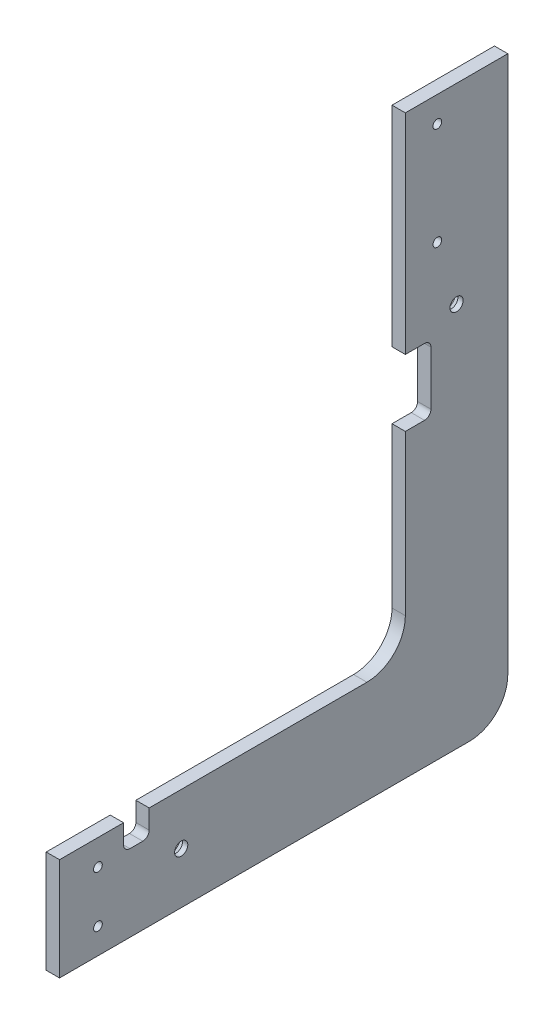
SolidWorks part; units mm, degrees
material "Acrylic (BLUE)"
ref_plane "Front Plane" through (0, 0, 0) normal (0, 0, 1) x (1, 0, 0)
ref_plane "Top Plane" through (0, 0, 0) normal (0, 1, 0) x (1, 0, 0)
ref_plane "Right Plane" through (0, 0, 0) normal (1, 0, 0) x (0, 0, -1)
sketch "Sketch1" plane through (0, 0, 0) normal (1, 0, 0) x (0, 0, -1)
  line L0 (-222.25, 0) -> (-171.45, 0)
  line L1 (-165.1, 0) -> (165.1, 0) construction
  line L2 (-165.1, 0) -> (-165.1, -228.6) construction
  line L3 (-165.1, -228.6) -> (165.1, -228.6) construction
  line L4 (165.1, 0) -> (165.1, -228.6) construction
  line L5 (171.45, 0) -> (222.25, 0)
  line L6 (-171.45, 0) -> (-171.45, -215.9)
  line L7 (-152.4, -234.95) -> (152.4, -234.95)
  line L8 (171.45, 0) -> (171.45, -215.9)
  line L9 (-165.1, 0) -> (-165.1, 25.4) construction
  line L10 (-222.25, 0) -> (-222.25, -266.7)
  line L11 (-203.2, -285.75) -> (203.2, -285.75)
  line L12 (222.25, 0) -> (222.25, -266.7)
  line L13 (-165.1, 25.4) -> (165.1, 25.4) construction
  line L14 (165.1, 25.4) -> (165.1, 0) construction
  line L15 (0, -234.95) -> (0, -285.75)
  arc A0 (203.2, -285.75) -> (222.25, -266.7) centre (203.2, -266.7) ccw
  arc A1 (-203.2, -285.75) -> (-222.25, -266.7) centre (-203.2, -266.7) cw
  arc A2 (171.45, -215.9) -> (152.4, -234.95) centre (152.4, -215.9) cw
  arc A3 (-152.4, -234.95) -> (-171.45, -215.9) centre (-152.4, -215.9) cw
  dimension "D8" = 19.05
  dimension "D1" = 50.8
  dimension "D2" = 330.2
  dimension "D3" = 228.6
  dimension "D4" = 6.35
  dimension "D5" = 6.35
  dimension "D6" = 6.35
  dimension "D7" = 50.8
  dimension "D9" = 254
  dimension "D10" = 25.4
  dimension "D11" = 285.75
extrude "Boss-Extrude2" add sketch "Sketch1" along normal blind 6.604 contours L8 A2 L7 L15 L11 A0 L12 L5
hole_wizard "CSK for #8 Flat Head Socket Cap Screw1" positions "Sketch4" profile "Sketch5" countersink size "#8" standard "ANSI Inch" end condition through all
sketch "Sketch4" plane through (0, -130.0171, -32.7853) normal (-1, 0, 0) x (0, 0, 1)
  line L15 (-154.5397, 117.3171) -> (-154.5397, 66.5171) construction
  line L16 (-154.5397, 66.5171) -> (-154.5397, 53.8171) construction
  line L18 (-154.5397, 117.3171) -> (-154.5397, 130.0171) construction
  line L20 (-138.6647, 130.0171) -> (-138.6647, -85.8829) construction
  line L21 (-138.6647, 130.0171) -> (-189.4647, 130.0171) construction
  point P37 (-154.5397, 117.3171)
  point P39 (-154.5397, 66.5171)
  dimension "D1" = 15.875
  dimension "D2" = 76.2
  dimension "D3" = 12.7
sketch "Sketch5" plane through (0, -12.7, -187.325) normal (0, 1, 0) x (0, 0, 1)
  line L0 (0, 0) -> (0, 6.604)
  line L1 (0, 6.604) -> (2.1526, 6.604)
  line L2 (2.1526, 6.604) -> (2.1526, 2.7685)
  line L3 (2.1526, 2.7685) -> (4.5593, 0)
  line L5 (4.5593, 0) -> (0, 0)
  line L6 (-2.1526, 2.7685) -> (-4.5593, 0) construction
  line L11 (0, -6.35) -> (0, 107.95) construction
  dimension "Thru Hole Dia." = 4.3053
  dimension "Thru Hole Depth" = 6.604
  dimension "Near C'Sink Dia." = 9.1186
  dimension "Near C'Sink Angle" = 82
hole_wizard "CSK for #8 Flat Head Socket Cap Screw2" positions "Sketch8" profile "Sketch7" countersink size "#8" standard "ANSI Inch" end condition through all
sketch "Sketch8" plane through (0, 131.5943, -188.0745) normal (-1, 0, 0) x (0, 0, 1)
  line L1 (169.0245, -366.5443) -> (169.0245, -379.2443) construction
  line L2 (188.0745, -366.5443) -> (35.6745, -366.5443) construction
  line L3 (169.0245, -379.2443) -> (169.0245, -404.6443) construction
  line L4 (169.0245, -404.6443) -> (169.0245, -417.3443) construction
  line L5 (188.0745, -417.3443) -> (-15.1255, -417.3443) construction
  line L6 (188.0745, -366.5443) -> (188.0745, -417.3443) construction
  point P3 (169.0245, -379.2443)
  point P7 (169.0245, -404.6443)
  dimension "D1" = 12.7
  dimension "D2" = 19.05
sketch "Sketch7" plane through (0, -247.65, -19.05) normal (0, 1, 0) x (0, 0, 1)
  line L0 (0, 0) -> (0, 6.604)
  line L1 (0, 6.604) -> (2.1526, 6.604)
  line L2 (2.1526, 6.604) -> (2.1526, 2.7685)
  line L3 (2.1526, 2.7685) -> (4.5593, 0)
  line L5 (4.5593, 0) -> (0, 0)
  line L6 (-2.1526, 2.7685) -> (-4.5593, 0) construction
  line L11 (0, -6.35) -> (0, 107.95) construction
  dimension "Thru Hole Dia." = 4.3053
  dimension "Thru Hole Depth" = 6.604
  dimension "Near C'Sink Dia." = 9.1186
  dimension "Near C'Sink Angle" = 82
hole_wizard "CSK for 1/4 Flat Head Socket Cap Screw1" positions "Sketch10" profile "Sketch9" countersink size "1/4" standard "ANSI Inch" end condition through all
sketch "Sketch10" plane through (0, -123.6761, -17.3866) normal (1, 0, 0) x (0, 0, -1)
  line L0 (179.4634, 123.6761) -> (179.4634, 28.8071) construction
  line L1 (154.0634, 123.6761) -> (204.8634, 123.6761) construction
  line L2 (-17.3866, -136.6739) -> (42.9384, -136.6739) construction
  line L3 (-17.3866, -111.2739) -> (-17.3866, -162.0739) construction
  point P1 (179.4634, 28.8071)
  point P4 (42.9384, -136.6739)
  dimension "D1" = 94.869
  dimension "D2" = 60.325
sketch "Sketch9" plane through (0, -94.869, -196.85) normal (0, 1, 0) x (0, 0, 1)
  line L0 (0, 0) -> (0, 6.604)
  line L1 (0, 6.604) -> (3.2639, 6.604)
  line L2 (3.2639, 6.604) -> (3.2639, 4.0031)
  line L3 (3.2639, 4.0031) -> (6.7437, 0)
  line L5 (6.7437, 0) -> (0, 0)
  line L6 (-3.2639, 4.0031) -> (-6.7437, 0) construction
  line L11 (0, -6.35) -> (0, 107.95) construction
  dimension "Thru Hole Dia." = 6.5278
  dimension "Thru Hole Depth" = 6.604
  dimension "Near C'Sink Dia." = 13.4874
  dimension "Near C'Sink Angle" = 82
sketch "Sketch11" plane through (0, 0, 0) normal (-1, 0, 0) x (0, 0, 1)
  line L0 (-171.45, 0) -> (-171.45, -215.9) construction
  line L1 (-171.45, -103.759) -> (-180.975, -103.759)
  line L2 (-171.45, -103.759) -> (-171.45, -136.779)
  line L3 (-171.45, -136.779) -> (-180.975, -136.779)
  line L4 (-184.15, -106.934) -> (-184.15, -133.604)
  line L6 (-171.45, -120.269) -> (-171.45, 0) construction
  line L7 (0, -234.95) -> (-152.4, -234.95) construction
  line L8 (-44.45, -234.95) -> (-31.75, -234.95)
  line L9 (-44.45, -234.95) -> (-44.45, -244.475)
  line L10 (-41.275, -247.65) -> (-34.925, -247.65)
  line L11 (-31.75, -234.95) -> (-31.75, -244.475)
  line L13 (-38.1, -234.95) -> (0, -234.95) construction
  line L14 (0, -234.95) -> (0, -285.75) construction
  arc A0 (-180.975, -136.779) -> (-184.15, -133.604) centre (-180.975, -133.604) cw
  arc A1 (-184.15, -106.934) -> (-180.975, -103.759) centre (-180.975, -106.934) cw
  arc A2 (-34.925, -247.65) -> (-31.75, -244.475) centre (-34.925, -244.475) ccw
  arc A3 (-41.275, -247.65) -> (-44.45, -244.475) centre (-41.275, -244.475) cw
  point P10 (-184.15, -136.779)
  point P13 (-184.15, -103.759)
  point P25 (-31.75, -247.65)
  point P28 (-44.45, -247.65)
  dimension "D4" = 3.175
  dimension "D8" = 3.175
  dimension "D1" = 12.7
  dimension "D2" = 33.02
  dimension "D3" = 120.269
  dimension "D5" = 12.7
  dimension "D6" = 12.7
  dimension "D7" = 38.1
extrude "Cut-Extrude1" cut sketch "Sketch11" against normal through all
other "Move Face1" [suppressed] parameters "D1"=0.0508
